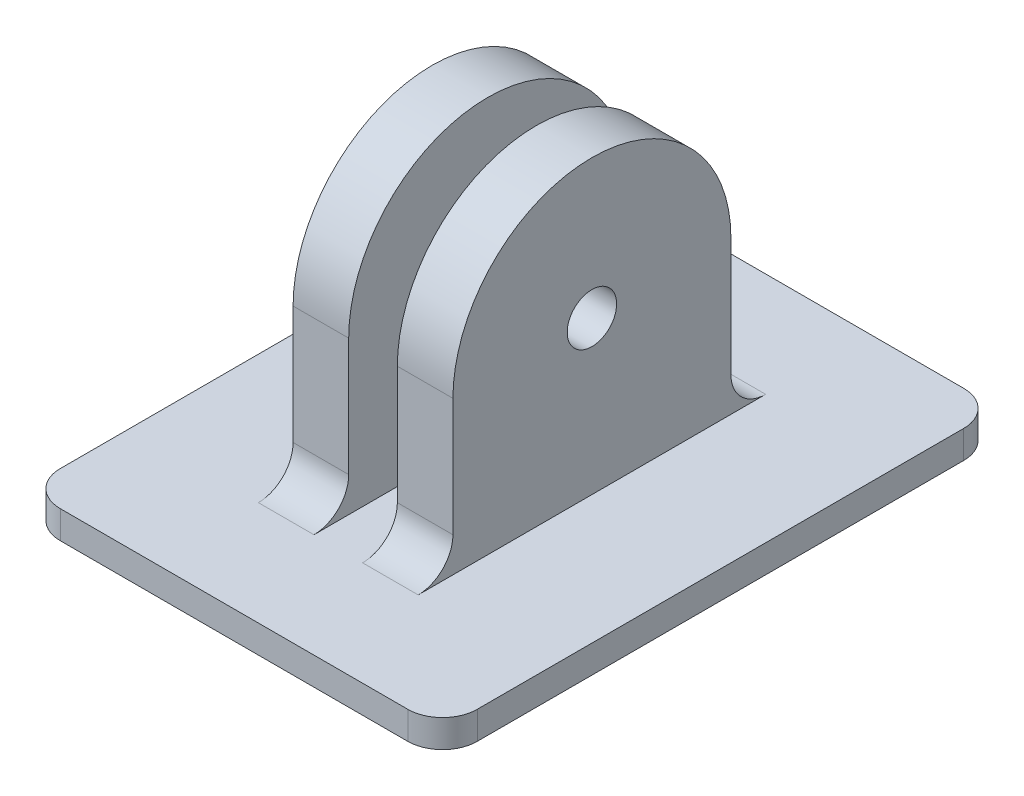
SolidWorks part; units mm, degrees
ref_plane "Plan de face" through (0, 0, 0) normal (0, 0, 1) x (1, 0, 0)
ref_plane "Plan de dessus" through (0, 0, 0) normal (0, 1, 0) x (1, 0, 0)
ref_plane "Plan de droite" through (0, 0, 0) normal (1, 0, 0) x (0, 0, -1)
sketch "Esquisse1" plane through (0, 0, 0) normal (0, 1, 0) x (1, 0, 0)
  line L1 (-15, 20) -> (15, 20)
  line L2 (-15, 20) -> (-15, -20)
  line L3 (-15, -20) -> (15, -20)
  line L4 (15, 20) -> (15, -20)
  point P4 (15, 0)
  point P6 (0, 20)
  dimension "D1" = 30
  dimension "D2" = 40
  dimension "D3" = 0
  dimension "D4" = 0
extrude "Boss.-Extru.1" add sketch "Esquisse1" along normal blind 2
sketch "Esquisse2" plane through (0, 2, 0) normal (0, 1, 0) x (1, 0, 0)
  line L0 (0, 0) -> (0, 10.1467) construction
  line L1 (1.75, 10) -> (5.75, 10)
  line L2 (1.75, 10) -> (1.75, -10)
  line L3 (1.75, -10) -> (5.75, -10)
  line L4 (5.75, 10) -> (5.75, -10)
  line L5 (-1.75, -10) -> (-5.75, -10)
  line L6 (-1.75, 10) -> (-5.75, 10)
  line L7 (-5.75, 10) -> (-5.75, -10)
  line L8 (-1.75, 10) -> (-1.75, -10)
  point P10 (1.75, 0)
  dimension "D1" = 1.75
  dimension "D2" = 20
  dimension "D3" = 4
  dimension "D4" = 0
extrude "Boss.-Extru.2" add sketch "Esquisse2" along normal blind 11
sketch "Esquisse3" plane through (-5.75, 0, 0) normal (-1, 0, 0) x (0, 0, 1)
  line L0 (-10, 13) -> (10, 13)
  arc A0 (-10, 13) -> (10, 13) centre (0, 13) cw
extrude "Boss.-Extru.3" add sketch "Esquisse3" against normal up to vertex
sketch "Esquisse4" plane through (5.75, 0, 0) normal (1, 0, 0) x (0, 0, -1)
  line L1 (10, 13) -> (-10, 13)
  arc A0 (-10, 13) -> (10, 13) centre (0, 13) cw
extrude "Boss.-Extru.4" add sketch "Esquisse4" against normal up to vertex
sketch "Esquisse5" plane through (5.75, 0, 0) normal (1, 0, 0) x (0, 0, -1)
  circle A0 centre (0, 13) radius 1.778
extrude "Enlèv. mat.-Extru.1" cut sketch "Esquisse5" against normal up to surface (11.5 mm away) up to face at (-5.75, 10, 0)
fillet "Congé1" radius 2.5 8 edges at (3.75, 2, -10) (15, 1, -20) (-15, 1, -20) (-3.75, 2, -10) (15, 1, 20) (-15, 1, 20) (3.75, 2, 10) (-3.75, 2, 10)
